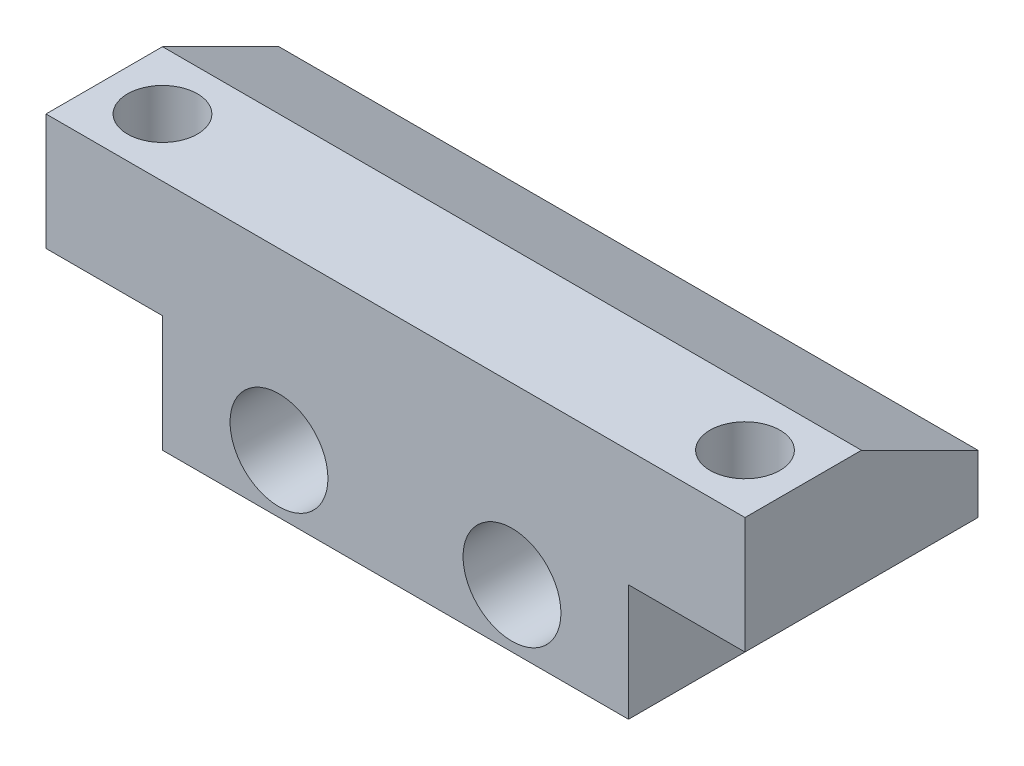
SolidWorks part; units mm, degrees
ref_plane "Front Plane" through (0, 0, 0) normal (0, 0, 1) x (1, 0, 0)
ref_plane "Top Plane" through (0, 0, 0) normal (0, 1, 0) x (1, 0, 0)
ref_plane "Right Plane" through (0, 0, 0) normal (1, 0, 0) x (0, 0, -1)
sketch "Sketch1" plane through (0, 0, 0) normal (0, 1, 0) x (1, 0, 0)
  line L1 (0, 0) -> (30, 0)
  line L2 (0, 0) -> (0, 10)
  line L3 (0, 10) -> (30, 10)
  line L4 (30, 0) -> (30, 10)
  dimension "D1" = 30
  dimension "D2" = 10
extrude "Boss-Extrude1" add sketch "Sketch1" along normal blind 5
sketch "Sketch2" plane through (0, 0, 0) normal (0, -1, 0) x (1, 0, 0)
  line L0 (0, 0) -> (30, 0) construction
  line L1 (5, 0) -> (25, 0)
  line L2 (5, 0) -> (5, -10)
  line L3 (5, -10) -> (25, -10)
  line L4 (25, 0) -> (25, -10)
  line L5 (0, -10) -> (0, 0) construction
  dimension "D1" = 20
  dimension "D2" = 5
  dimension "D3" = 10
extrude "Boss-Extrude2" add sketch "Sketch2" along normal blind 5
sketch "Sketch3" plane through (0, 0, 0) normal (0, 0, 1) x (1, 0, 0)
  line L0 (25, -5) -> (5, -5) construction
  line L1 (25, -5) -> (25, 0) construction
  circle A0 centre (20, -2.5) radius 2.1
  dimension "D1" = 4.2
  dimension "D2" = 2.5
  dimension "D3" = 5
extrude "Cut-Extrude1" cut sketch "Sketch3" against normal blind 10
pattern_linear "LPattern1" count 2 spacing 10 along (-1, 0, 0) of "Cut-Extrude1"
sketch "Sketch4" plane through (0, 5, 0) normal (0, 1, 0) x (1, 0, 0)
  line L0 (0, 0) -> (30, 0) construction
  line L1 (30, 0) -> (30, 10) construction
  circle A0 centre (27.5, 2.5) radius 1.5
  dimension "D1" = 3
  dimension "D2" = 2.5
  dimension "D3" = 2.5
extrude "Cut-Extrude2" cut sketch "Sketch4" against normal blind 5
pattern_linear "LPattern2" count 2 spacing 25 along (-1, 0, 0) of "Cut-Extrude2"
sketch "Sketch5" plane through (0, -5, 0) normal (0, -1, 0) x (1, 0, 0)
  line L0 (5, -10) -> (25, -10) construction
  line L1 (14.25, -10) -> (15.75, -10)
  line L2 (14.25, -10) -> (14.25, -8.5)
  line L3 (14.25, -8.5) -> (15.75, -8.5)
  line L4 (15.75, -10) -> (15.75, -8.5)
  line L5 (15, 0) -> (15, -10) construction
  line L6 (25, 0) -> (5, 0) construction
  dimension "D1" = 0.75
  dimension "D2" = 1.5
  dimension "D3" = 1.5
extrude "Cut-Extrude3" cut sketch "Sketch5" against normal blind 5
chamfer "Chamfer1" distance 2.5 distance2 5 1 edges at (15, 5, -10)
